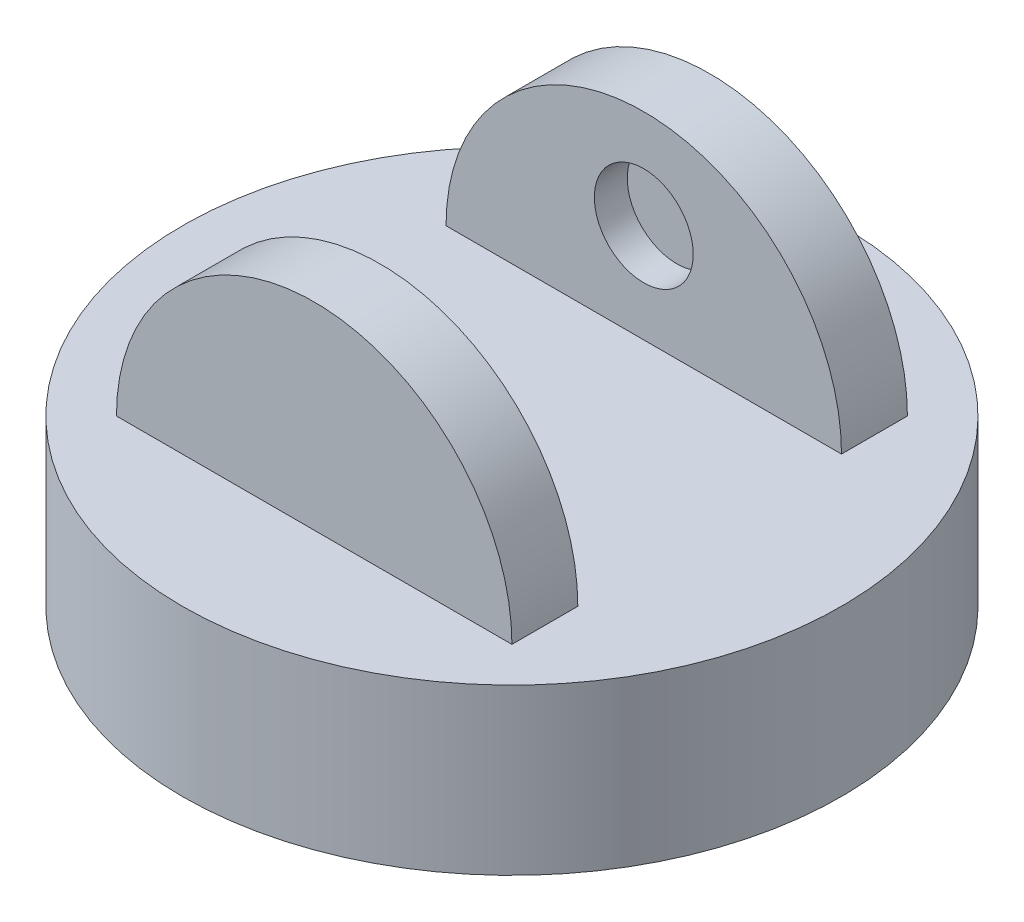
SolidWorks part; units mm, degrees
ref_plane "Front Plane" through (0, 0, 0) normal (0, 0, 1) x (1, 0, 0)
ref_plane "Top Plane" through (0, 0, 0) normal (0, 1, 0) x (1, 0, 0)
ref_plane "Right Plane" through (0, 0, 0) normal (1, 0, 0) x (0, 0, -1)
sketch "Sketch1" plane through (0, 0, 0) normal (0, 1, 0) x (1, 0, 0)
  circle A0 centre (0, 0) radius 100
  dimension "D1" = 200
extrude "Boss-Extrude1" add sketch "Sketch1" along normal blind 50
sketch "Sketch2" plane through (0, 0, 0) normal (0, 0, 1) x (1, 0, 0)
  line L0 (100, 50) -> (-100, 50) construction
  line L1 (-60, 50) -> (0, 50)
  line L2 (0, 50) -> (60, 50)
  arc A0 (-60, 50) -> (60, 50) centre (0, 50) cw
  point P3 (0, 0)
  dimension "D2" = 60
  dimension "D1" = 0
extrude "Boss-Extrude2" add sketch "Sketch2" along normal blind 60
sketch "Sketch6" plane through (0, 0, 0) normal (0, 0, -1) x (-1, 0, 0)
  line L0 (-60, 50) -> (60, 50)
  line L2 (-60, 50) -> (60, 50)
  line L3 (-60, 50) -> (60, 50)
  arc A1 (60, 50) -> (-60, 50) centre (0, 50) ccw
  arc M3 (60, 50) -> (-60, 50) centre (0, 50) ccw
  line M4 (-60, 50) -> (60, 50)
  dimension "D1" = 0
extrude "Boss-Extrude4" add sketch "Sketch6" along normal blind 60 contours M4 M3
sketch "Sketch9" plane through (0, 50, 0) normal (0, 1, 0) x (1, 0, 0)
  line L1 (60, 40) -> (-60, 40)
  line L2 (60, 40) -> (60, -40)
  line L3 (60, -40) -> (-60, -40)
  line L4 (-60, 40) -> (-60, -40)
  line L5 (60, 40) -> (-60, -40) construction
  line L6 (60, -40) -> (-60, 40) construction
  point P0 (0, 0)
  dimension "D1" = 120
  dimension "D2" = 80
extrude "Cut-Extrude1" cut sketch "Sketch9" along normal blind 68
sketch "Sketch15" plane through (0, 0, 40) normal (0, 0, -1) x (-1, 0, 0)
  circle A0 centre (0, 80) radius 15
  dimension "D1" = 30
  dimension "D2" = 80
extrude "Cut-Extrude3" cut sketch "Sketch15" against normal blind 10
sketch "Sketch19" plane through (0, 0, -40) normal (0, 0, 1) x (1, 0, 0)
  circle A0 centre (0, 80) radius 15
  arc A1 (60, 50) -> (-60, 50) centre (0, 50) ccw construction
  dimension "D1" = 30
  dimension "D2" = 30
extrude "Cut-Extrude4" cut sketch "Sketch19" against normal blind 10
